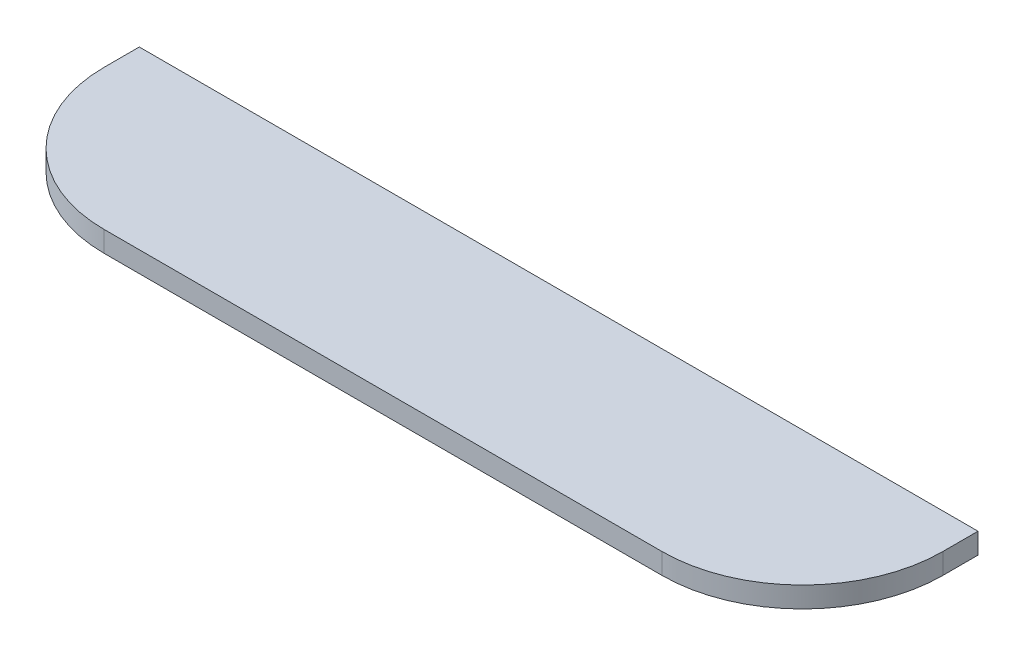
SolidWorks part; units mm, degrees
material "Acrylic (Medium-high impact)"
ref_plane "Front Plane" through (0, 0, 0) normal (0, 0, 1) x (1, 0, 0)
ref_plane "Top Plane" through (0, 0, 0) normal (0, 1, 0) x (1, 0, 0)
ref_plane "Right Plane" through (0, 0, 0) normal (1, 0, 0) x (0, 0, -1)
sketch "Sketch1" plane through (0, 0, 0) normal (0, 0, 1) x (1, 0, 0)
  line L1 (-60.665, 1.5) -> (60.665, 1.5)
  line L2 (-60.665, 1.5) -> (-60.665, -1.5)
  line L3 (-60.665, -1.5) -> (60.665, -1.5)
  line L4 (60.665, 1.5) -> (60.665, -1.5)
  line L5 (-60.665, 1.5) -> (60.665, -1.5) construction
  line L6 (-60.665, -1.5) -> (60.665, 1.5) construction
  point P0 (0, 0)
  dimension "D1" = 3
  dimension "D2" = 121.33
extrude "Boss-Extrude1" add sketch "Sketch1" along normal blind 25.4
fillet "Fillet1" radius 20.32 2 edges at (60.665, 0, 25.4) (-60.665, 0, 25.4)
